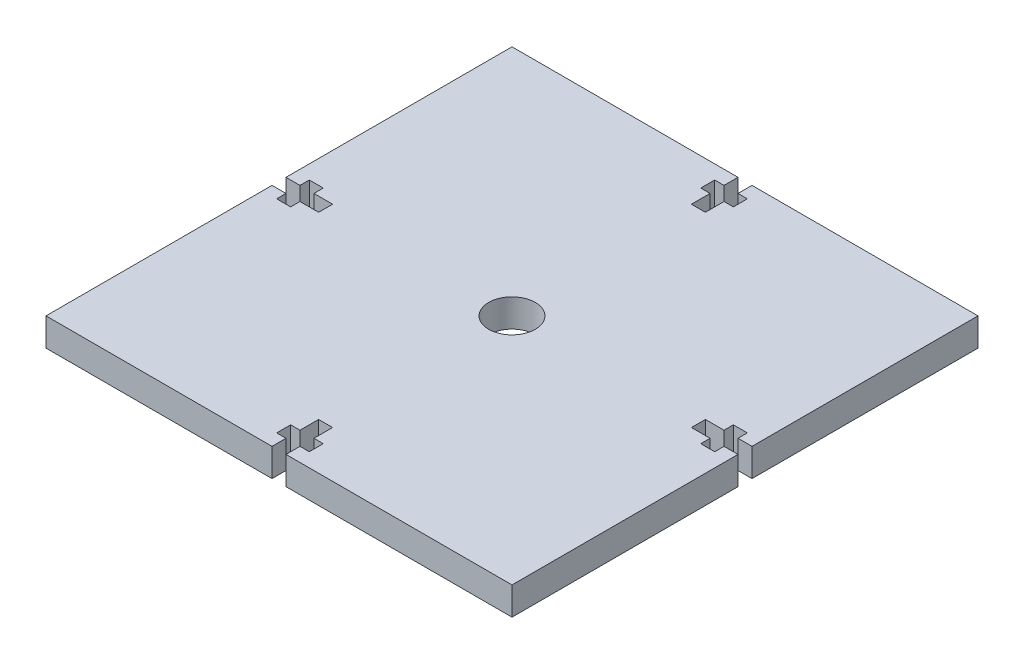
SolidWorks part; units mm, degrees
ref_plane "Front Plane" through (0, 0, 0) normal (0, 0, 1) x (1, 0, 0)
ref_plane "Top Plane" through (0, 0, 0) normal (0, 1, 0) x (1, 0, 0)
ref_plane "Right Plane" through (0, 0, 0) normal (1, 0, 0) x (0, 0, -1)
sketch "Sketch1" plane through (0, 0, 0) normal (0, 1, 0) x (1, 0, 0)
  line L0 (0, 0) -> (100, 0)
  line L1 (100, 0) -> (100, -100)
  line L2 (100, -100) -> (0, -100)
  line L3 (0, -100) -> (0, 0)
extrude "Boss-Extrude1" add sketch "Sketch1" along normal blind 6
sketch "Sketch2" plane through (0, 6, 0) normal (0, 1, 0) x (1, 0, 0)
  line L0 (50, 0) -> (50, -100) construction
  line L1 (100, 0) -> (0, 0) construction
  line L2 (0, -100) -> (100, -100) construction
  line L3 (0, -50) -> (100, -50) construction
  line L4 (0, 0) -> (0, -100) construction
  line L5 (100, -100) -> (100, 0) construction
  line L6 (48.5, 0) -> (51.5, 0)
  line L7 (51.5, 0) -> (51.5, -3)
  line L8 (51.5, -3) -> (53.5, -3)
  line L9 (53.5, -3) -> (53.5, -6)
  line L10 (53.5, -6) -> (51.5, -6)
  line L11 (51.5, -6) -> (51.5, -10)
  line L12 (51.5, -10) -> (48.5, -10)
  line L13 (48.5, -6) -> (48.5, -10)
  line L14 (46.5, -6) -> (48.5, -6)
  line L15 (46.5, -3) -> (46.5, -6)
  line L16 (48.5, -3) -> (46.5, -3)
  line L17 (48.5, 0) -> (48.5, -3)
  line L18 (48.5, -100) -> (48.5, -97)
  line L19 (48.5, -97) -> (46.5, -97)
  line L20 (46.5, -97) -> (46.5, -94)
  line L21 (46.5, -94) -> (48.5, -94)
  line L22 (48.5, -94) -> (48.5, -90)
  line L23 (51.5, -90) -> (48.5, -90)
  line L24 (51.5, -94) -> (51.5, -90)
  line L25 (53.5, -94) -> (51.5, -94)
  line L26 (53.5, -97) -> (53.5, -94)
  line L27 (51.5, -97) -> (53.5, -97)
  line L28 (51.5, -100) -> (51.5, -97)
  line L29 (48.5, -100) -> (51.5, -100)
  point P20 (50, -10)
  point P37 (50, -90)
extrude "Cut-Extrude1" cut sketch "Sketch2" against normal through all
sketch "Sketch3" plane through (0, 0, 0) normal (0, -1, 0) x (1, 0, 0)
  line L0 (50, 90) -> (50, 10) construction
  line L1 (51.5, 90) -> (48.5, 90) construction
  line L2 (48.5, 10) -> (51.5, 10) construction
  line L3 (0, 50) -> (100, 50) construction
  line L4 (0, 0) -> (0, 100) construction
  line L5 (100, 100) -> (100, 0) construction
  circle A0 centre (50, 50) radius 5
extrude "Cut-Extrude2" cut sketch "Sketch3" against normal blind 10
sketch "Sketch5" plane through (0, 6, 0) normal (0, 1, 0) x (1, 0, 0)
  line L0 (100, 0) -> (100, -100) construction
  line L1 (0, 0) -> (0, -100) construction
  line L3 (0, -48.5) -> (3, -48.5)
  line L4 (3, -48.5) -> (3, -46.5)
  line L5 (3, -46.5) -> (6, -46.5)
  line L6 (6, -46.5) -> (6, -48.5)
  line L7 (6, -48.5) -> (10, -48.5)
  line L8 (10, -48.5) -> (10, -50)
  line L14 (0, 0) -> (100, 0) construction
  line L15 (50, 0) -> (50, -100) construction
  line L16 (100, -50) -> (100, -48.5)
  line L17 (100, -48.5) -> (97, -48.5)
  line L18 (97, -46.5) -> (97, -48.5)
  line L19 (97, -46.5) -> (94, -46.5)
  line L20 (94, -46.5) -> (94, -48.5)
  line L21 (94, -48.5) -> (90, -48.5)
  line L22 (90, -48.5) -> (90, -50)
  line L24 (100, -50) -> (0, -50) construction
  line L25 (100, -50) -> (100, -51.5)
  line L26 (100, -51.5) -> (97, -51.5)
  line L27 (97, -51.5) -> (97, -53.5)
  line L28 (97, -53.5) -> (94, -53.5)
  line L29 (94, -53.5) -> (94, -51.5)
  line L30 (94, -51.5) -> (90, -51.5)
  line L31 (90, -51.5) -> (90, -50)
  line L33 (0, -51.5) -> (3, -51.5)
  line L34 (3, -51.5) -> (3, -53.5)
  line L35 (3, -53.5) -> (6, -53.5)
  line L36 (6, -53.5) -> (6, -51.5)
  line L37 (6, -51.5) -> (10, -51.5)
  line L38 (10, -51.5) -> (10, -50)
extrude "Cut-Extrude6" cut sketch "Sketch5" against normal through all contours L37 L38 L8 L7 L6 L5 L4 L3 L24 L33 L34 L35 L36 | L31 L30 L29 L28 L27 L26 L37 L17 L18 L19 L20 L21 L22
